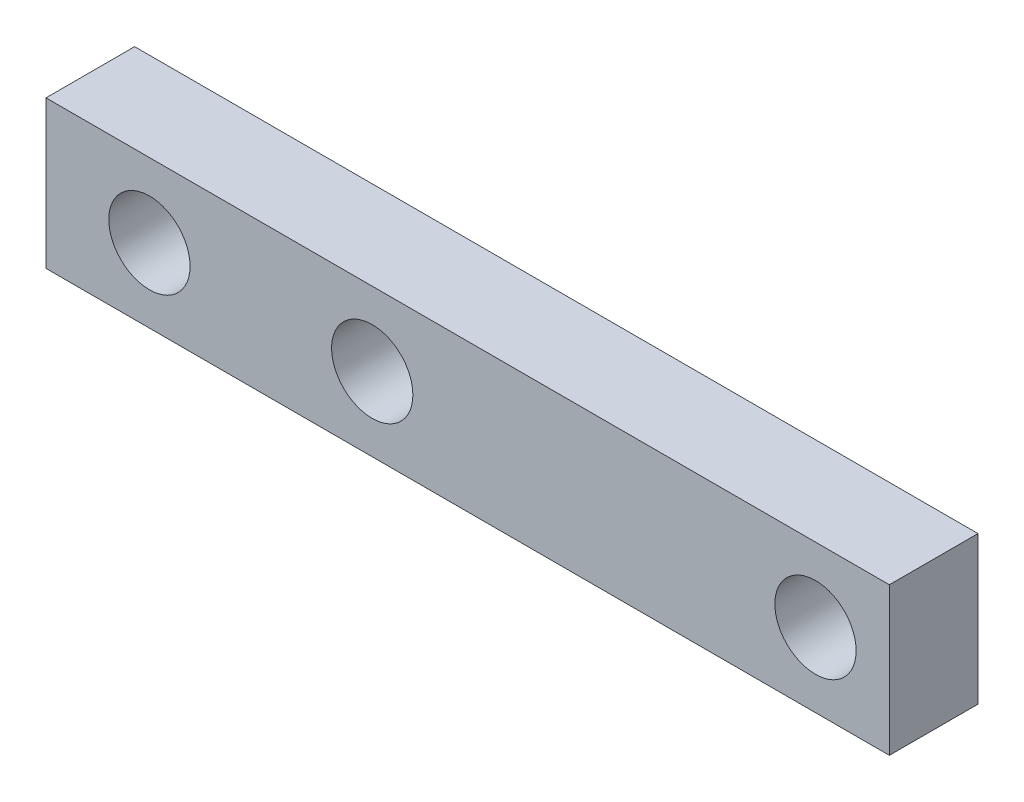
SolidWorks part; units mm, degrees
ref_plane "Front Plane" through (0, 0, 0) normal (0, 0, 1) x (1, 0, 0)
ref_plane "Top Plane" through (0, 0, 0) normal (0, 1, 0) x (1, 0, 0)
ref_plane "Right Plane" through (0, 0, 0) normal (1, 0, 0) x (0, 0, -1)
sketch "Sketch2" plane through (0, 0, 0) normal (0, 0, 1) x (1, 0, 0)
  line L0 (0, 0) -> (0, 5)
  line L1 (0, 5) -> (28.54, 5)
  line L2 (28.54, 5) -> (28.54, 0)
  line L3 (28.54, 0) -> (0, 0)
  circle A0 centre (3.5, 2.5) radius 1.375
  circle A1 centre (11.04, 2.5) radius 1.375
  circle A2 centre (26.04, 2.5) radius 1.375
  dimension "D3" = 2.75
  dimension "D5" = 2.5
  dimension "D6" = 2.75
  dimension "D8" = 2.75
  dimension "D1" = 15
  dimension "D2" = 5
  dimension "D4" = 3.5
  dimension "D7" = 7.54
  dimension "D9" = 2.5
extrude "Boss-Extrude1" add sketch "Sketch2" along normal blind 3
